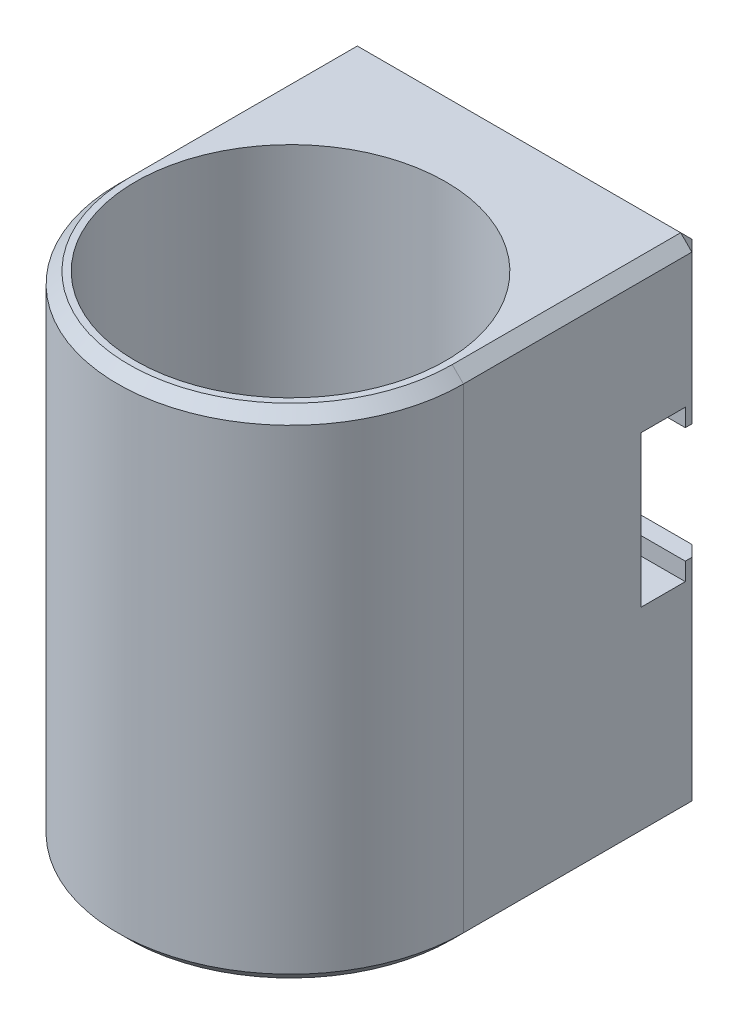
SolidWorks part; units mm, degrees
ref_plane "Front Plane" through (0, 0, 0) normal (0, 0, 1) x (1, 0, 0)
ref_plane "Top Plane" through (0, 0, 0) normal (0, 1, 0) x (1, 0, 0)
ref_plane "Right Plane" through (0, 0, 0) normal (1, 0, 0) x (0, 0, -1)
sketch "Sketch1" plane through (0, 0, 0) normal (0, 1, 0) x (1, 0, 0)
  line L0 (-15.4375, 0) -> (-15.4375, 21.4)
  line L1 (-15.4375, 21.4) -> (15.4375, 21.4)
  line L2 (15.4375, 21.4) -> (15.4375, 0)
  circle A0 centre (0, 0) radius 13.85
  circle A1 centre (0, 0) radius 15.4375 construction
  arc A2 (-15.4375, 0) -> (15.4375, 0) centre (0, 0) ccw
  dimension "D1" = 27.7
  dimension "D2" = 1.5875
  dimension "D3" = 21.4
extrude "Boss-Extrude1" add sketch "Sketch1" along normal blind 44.45
sketch "Sketch2" plane through (0, 0, 0) normal (0, -1, 0) x (1, 0, 0)
  circle A0 centre (0, 0) radius 15.0813
  dimension "D1" = 30.1625
extrude "Boss-Extrude2" add sketch "Sketch2" against normal blind 1.5875
sketch "Sketch3" plane through (15.4375, 0, 0) normal (1, 0, 0) x (0, 0, -1)
  line L0 (21.4, 30.1625) -> (19.8125, 30.1625)
  line L1 (21.4, 44.45) -> (21.4, 0) construction
  line L2 (19.8125, 30.1625) -> (19.8125, 31.75)
  line L3 (19.8125, 31.75) -> (15.8438, 31.75)
  line L4 (15.8438, 31.75) -> (15.8438, 18.2563)
  line L5 (15.8438, 18.2563) -> (19.8125, 18.2563)
  line L6 (19.8125, 18.2563) -> (19.8125, 19.8438)
  line L7 (19.8125, 19.8438) -> (21.4, 19.8438)
  line L8 (21.4, 19.8438) -> (21.4, 30.1625)
  line L9 (0, 44.45) -> (21.4, 44.45) construction
  dimension "D1" = 1.5875
  dimension "D2" = 3.9688
  dimension "D3" = 13.4937
  dimension "D4" = 1.5875
  dimension "D5" = 12.7
extrude "Cut-Extrude1" cut sketch "Sketch3" against normal through all
chamfer "Chamfer1" distance 1 angle 45 12 edges at (-15.4375, 9.9219, -21.4) (15.4375, 9.9219, -21.4) (0, 0, -21.4) (-15.4375, 0, -10.7) (0, 0, 15.4375) (15.4375, 0, -10.7) (-15.4375, 37.3062, -21.4) (15.4375, 37.3062, -21.4) (0, 44.45, -21.4) (-15.4375, 44.45, -10.7) (0, 44.45, 15.4375) (15.4375, 44.45, -10.7)
